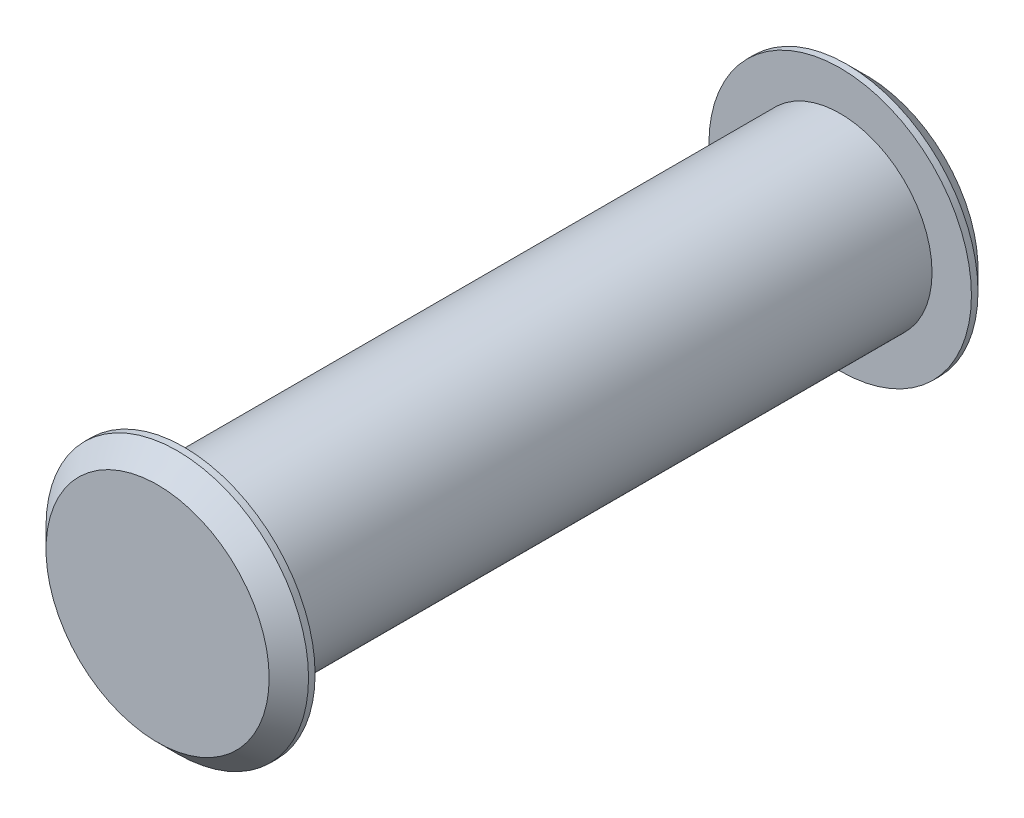
SolidWorks part; units mm, degrees
ref_plane "Płaszczyzna przednia" through (0, 0, 0) normal (0, 0, 1) x (1, 0, 0)
ref_plane "Płaszczyzna górna" through (0, 0, 0) normal (0, 1, 0) x (1, 0, 0)
ref_plane "Płaszczyzna prawa" through (0, 0, 0) normal (1, 0, 0) x (0, 0, -1)
sketch "Sketch1" plane through (0, 0, 0) normal (0, 0, 1) x (1, 0, 0)
  circle A0 centre (0, 0) radius 3.5
  dimension "D1" = 7
extrude "Boss-Extrude1" add sketch "Sketch1" along normal mid plane 25
sketch "Sketch2" plane through (0, 0, 12.5) normal (0, 0, 1) x (1, 0, 0)
  circle A0 centre (0, 0) radius 5
  dimension "D1" = 10
extrude "Boss-Extrude2" add sketch "Sketch2" along normal blind 1
mirror "Mirror1" about plane through (0, 0, 0) normal (0, 0, 1) of "Boss-Extrude2"
chamfer "Chamfer1" distance 0.75 angle 45 2 edges at (5, 0, -13.5) (5, 0, 13.5)
